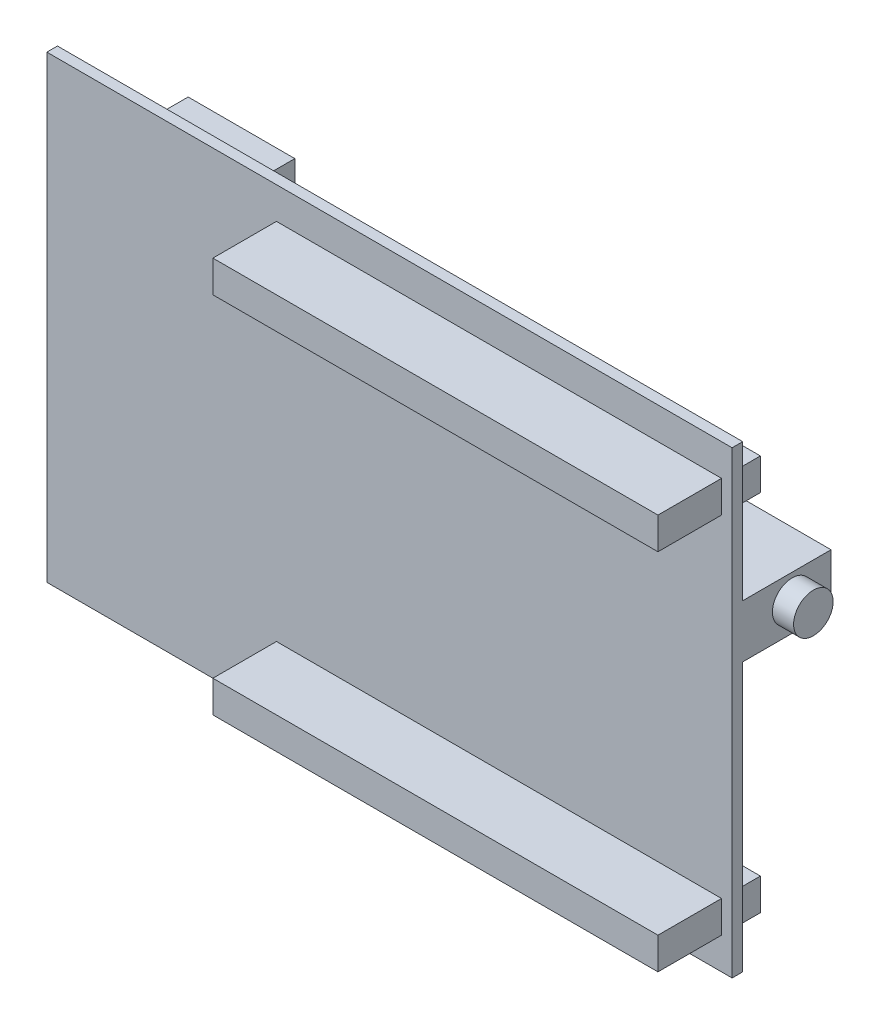
SolidWorks part; units mm, degrees
ref_plane "Ön Düzlem" through (0, 0, 0) normal (0, 0, 1) x (1, 0, 0)
ref_plane "Üst Düzlem" through (0, 0, 0) normal (0, 1, 0) x (1, 0, 0)
ref_plane "Sağ Düzlem" through (0, 0, 0) normal (1, 0, 0) x (0, 0, -1)
sketch "Sketch1" plane through (0, 0, 0) normal (0, 0, 1) x (1, 0, 0)
  line L1 (-48.5, 32.5) -> (48.5, 32.5)
  line L2 (-48.5, 32.5) -> (-48.5, -32.5)
  line L3 (-48.5, -32.5) -> (48.5, -32.5)
  line L4 (48.5, 32.5) -> (48.5, -32.5)
  line L5 (-48.5, 32.5) -> (48.5, -32.5) construction
  line L6 (-48.5, -32.5) -> (48.5, 32.5) construction
  point P0 (0, 0)
  dimension "D1" = 97
  dimension "D2" = 65
extrude "Boss-Extrude1" add sketch "Sketch1" along normal blind 1.5 contours L1 L4 L3 L2
sketch "Sketch2" plane through (0, 0, 0) normal (0, 0, -1) x (-1, 0, 0)
  line L0 (-47, 28) -> (-47, 23.5)
  line L1 (48.5, 32.5) -> (-48.5, 32.5) construction
  line L2 (-48.5, 32.5) -> (-48.5, -32.5) construction
  line L3 (-47, 23.5) -> (16, 23.5)
  line L4 (16, 23.5) -> (16, 28)
  line L5 (16, 28) -> (-47, 28)
  line L6 (-63.3127, 0) -> (59.1173, 0) construction
  line L7 (16, -28) -> (-47, -28)
  line L8 (16, -23.5) -> (16, -28)
  line L9 (-47, -23.5) -> (16, -23.5)
  line L10 (-47, -28) -> (-47, -23.5)
  dimension "D1" = 1.5
  dimension "D2" = 4.5
  dimension "D3" = 4.5
  dimension "D4" = 63
extrude "Boss-Extrude2" add sketch "Sketch2" along normal blind 4 and the other way blind 10.5
sketch "Sketch3" plane through (0, 0, 0) normal (0, 0, -1) x (-1, 0, 0)
  line L0 (-48.5, 13) -> (-48.5, 5.5)
  line L1 (-48.5, 32.5) -> (-48.5, -32.5) construction
  line L2 (-48.5, 5.5) -> (-35, 5.5)
  line L3 (-35, 5.5) -> (-35, 13)
  line L4 (-35, 13) -> (-48.5, 13)
extrude "Boss-Extrude3" add sketch "Sketch3" along normal blind 12.5
sketch "Sketch4" plane through (48.5, 0, 0) normal (1, 0, 0) x (0, 0, -1)
  circle A0 centre (7, 9.5) radius 2.8
extrude "Boss-Extrude4" add sketch "Sketch4" along normal blind 3
sketch "Sketch5" plane through (0, 0, 0) normal (0, 0, -1) x (-1, 0, 0)
  line L0 (48.5, 0) -> (56.2577, 0) construction
  line L1 (48.5, 32.5) -> (48.5, -32.5) construction
  line L2 (46.5, -26.8302) -> (46.5, -25.3302)
  line L3 (46.5, 25.3302) -> (42, 25.3302)
  line L4 (42, 25.3302) -> (42, 26.8302)
  line L5 (42, 26.8302) -> (46.5, 26.8302)
  line L6 (46.5, 26.8302) -> (46.5, 25.3302)
  line L7 (42, -26.8302) -> (46.5, -26.8302)
  line L8 (42, -25.3302) -> (42, -26.8302)
  line L9 (46.5, -25.3302) -> (42, -25.3302)
  dimension "D1" = 5.6698
extrude "Boss-Extrude5" add sketch "Sketch5" along normal up to surface (4 mm away) up to face at (15.5, -25.75, -4)
sketch "Sketch6" plane through (0, 0, 0) normal (0, 0, -1) x (-1, 0, 0)
  line L3 (38.5, 27) -> (38.5, 24)
  line L4 (38.5, 24) -> (23.4, 24)
  line L5 (23.4, 24) -> (23.4, 27)
  line L6 (23.4, 27) -> (38.5, 27)
extrude "Boss-Extrude6" add sketch "Sketch6" along normal blind 8.5 contours L4 L5 L6 L3
sketch "Sketch7" plane through (0, 0, 0) normal (0, 0, -1) x (-1, 0, 0)
  line L3 (33.5, -16.5) -> (33.5, -14.5)
  line L4 (33.5, -14.5) -> (23.5, -14.5)
  line L5 (23.5, -14.5) -> (23.5, -16.5)
  line L6 (23.5, -16.5) -> (33.5, -16.5)
  point P0 (0, 0)
  dimension "D1" = 16
  dimension "D2" = 15
  dimension "D3" = 10
  dimension "D4" = 2
extrude "Boss-Extrude7" add sketch "Sketch7" along normal up to surface (8.5 mm away) up to face at (-30.95, 25.5, -8.5)
sketch "Sketch8" plane through (0, 0, 0) normal (0, 0, -1) x (-1, 0, 0)
  line L0 (48.5, 32.5) -> (48.5, -32.5) construction
  line L3 (9, 16.5) -> (9, 14.5)
  line L4 (9, 14.5) -> (3.5, 14.5)
  line L5 (3.5, 14.5) -> (3.5, 16.5)
  line L6 (3.5, 16.5) -> (9, 16.5)
  point P3 (0, 0)
  point P4 (8.888, 16.5)
  dimension "D1" = 16
  dimension "D2" = 39.5
  dimension "D3" = 5.5
  dimension "D4" = 2
extrude "Boss-Extrude8" add sketch "Sketch8" along normal up to surface (8.5 mm away) contours L6 L3 L4 L5 up to face at (-30.95, 25.5, -8.5)
sketch "Sketch9" plane through (0, 0, 0) normal (0, 0, -1) x (-1, 0, 0)
  line L0 (0, 0) -> (-22.3078, 0) construction
  line L1 (-19.5, -17.5) -> (-13.5, -17.5)
  line L2 (-13.5, 17.5) -> (-13.5, 11.5)
  line L3 (-13.5, 11.5) -> (-19.5, 11.5)
  line L4 (-19.5, 11.5) -> (-19.5, 17.5)
  line L5 (-19.5, 17.5) -> (-13.5, 17.5)
  line L6 (-19.5, -11.5) -> (-19.5, -17.5)
  line L7 (-13.5, -11.5) -> (-19.5, -11.5)
  line L8 (-13.5, -17.5) -> (-13.5, -11.5)
  dimension "D1" = 17
  dimension "D2" = 1
  dimension "D3" = 6
  dimension "D4" = 6
extrude "Boss-Extrude9" add sketch "Sketch9" along normal blind 4 contours L1 L8 L7 L6 | L2 L3 L4 L5
ref_point "Point1"
sketch "Sketch10" plane through (0, 0, -4) normal (0, 0, -1) x (-1, 0, 0)
  circle A0 centre (-16.5, 14.5) radius 2.5
extrude "Boss-Extrude10" add sketch "Sketch10" along normal blind 6
ref_point "Point2"
sketch "Sketch13" plane through (0, 0, -4) normal (0, 0, -1) x (-1, 0, 0)
  circle A0 centre (-16.5, -14.5) radius 2.5
extrude "Boss-Extrude11" add sketch "Sketch13" along normal up to surface (6 mm away) up to face at (14, 14.5, -10)
